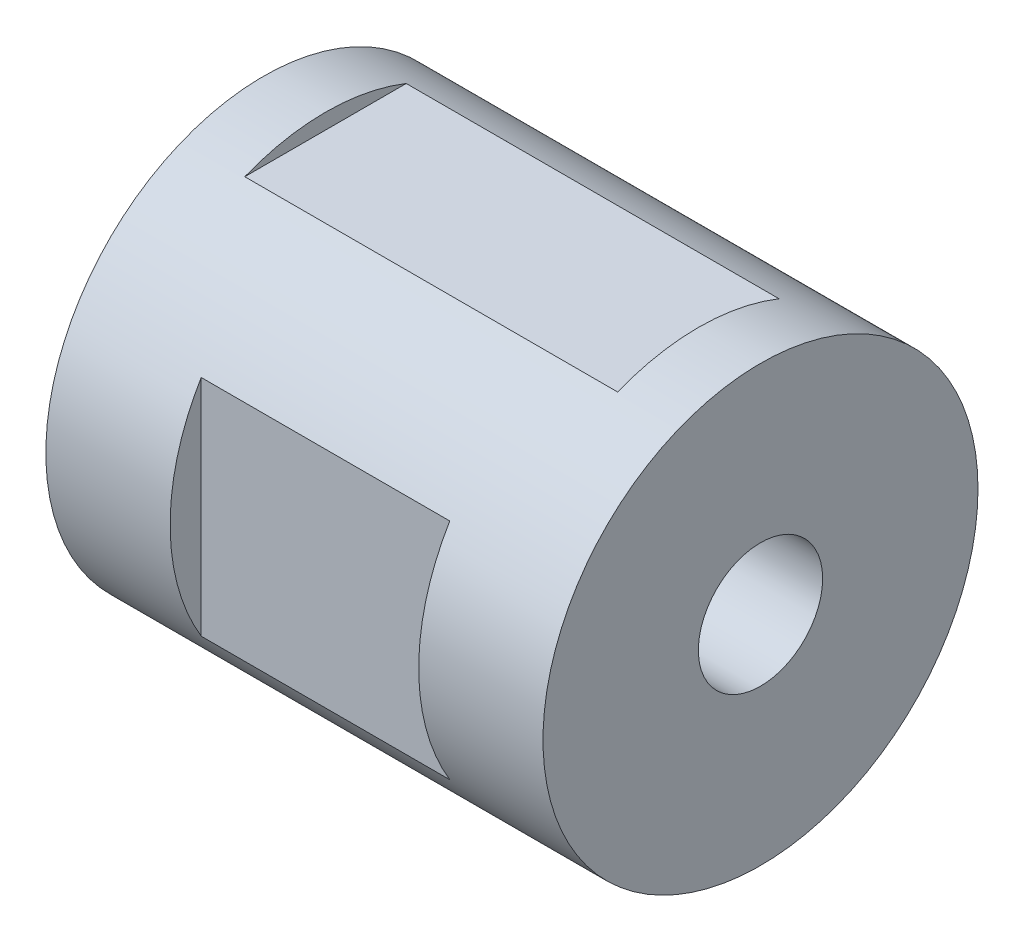
SolidWorks part; units mm, degrees
ref_plane "Front Plane" through (0, 0, 0) normal (0, 0, 1) x (1, 0, 0)
ref_plane "Top Plane" through (0, 0, 0) normal (0, 1, 0) x (1, 0, 0)
ref_plane "Right Plane" through (0, 0, 0) normal (1, 0, 0) x (0, 0, -1)
sketch "Sketch5" plane through (0, 0, 0) normal (1, 0, 0) x (0, 0, -1)
  circle A0 centre (0, 0) radius 35
  circle A1 centre (0, 0) radius 10
  dimension "D1" = 20
  dimension "D2" = 70
extrude "Boss-Extrude2" add sketch "Sketch5" against normal blind 80
ref_plane "Top Cut" through (0, 32.5, 0) normal (0, 1, 0) x (1, 0, 0)
sketch "Sketch6" plane through (0, 32.5, 0) normal (0, 1, 0) x (1, 0, 0)
  line L0 (-80, -35) -> (0, -35) construction
  line L1 (-70, 12.99) -> (-10, 12.99)
  line L2 (-70, 12.99) -> (-70, -12.99)
  line L3 (-70, -12.99) -> (-10, -12.99)
  line L4 (-10, 12.99) -> (-10, -12.99)
  line L5 (0, -35) -> (0, 35) construction
  dimension "D1" = 60
  dimension "D2" = 25.98
  dimension "D3" = 22.01
  dimension "D4" = 10
extrude "Cut-Extrude3" cut sketch "Sketch6" along normal blind 10
ref_plane "Side Cut" through (0, 0, 30) normal (0, 0, 1) x (1, 0, 0)
sketch "Sketch7" plane through (0, 0, 30) normal (0, 0, 1) x (1, 0, 0)
  line L0 (0, -35) -> (0, 35) construction
  line L1 (-60, 18.03) -> (-20, 18.03)
  line L2 (-60, 18.03) -> (-60, -18.03)
  line L3 (-60, -18.03) -> (-20, -18.03)
  line L4 (-20, 18.03) -> (-20, -18.03)
  line L5 (-80, -35) -> (0, -35) construction
  dimension "D1" = 36.06
  dimension "D2" = 40
  dimension "D3" = 20
  dimension "D4" = 16.97
extrude "Cut-Extrude4" cut sketch "Sketch7" along normal blind 10
